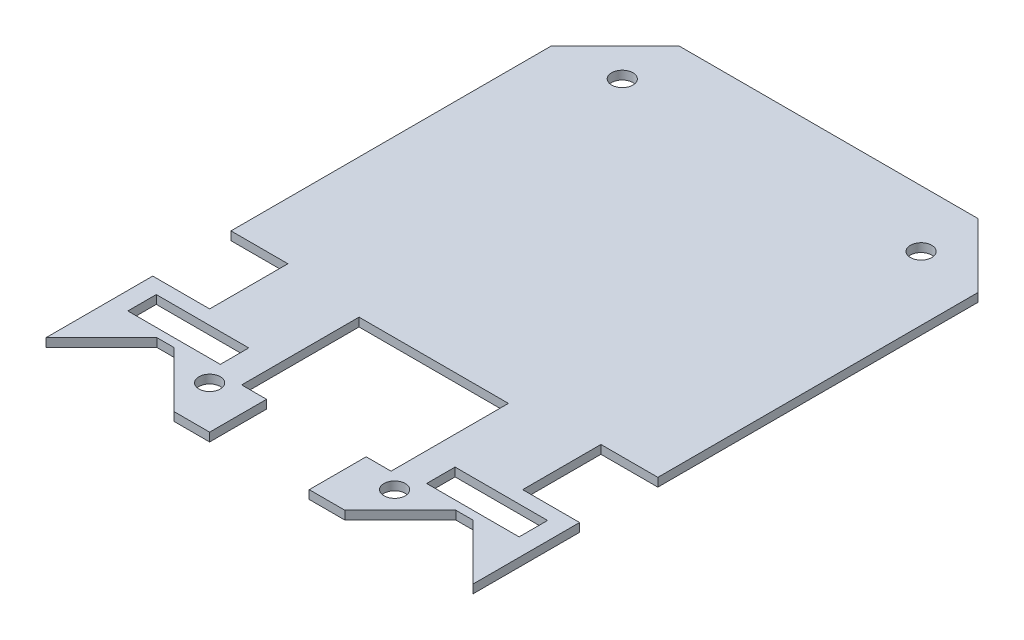
SolidWorks part; units mm, degrees
ref_plane "Front Plane" through (0, 0, 0) normal (0, 0, 1) x (1, 0, 0)
ref_plane "Top Plane" through (0, 0, 0) normal (0, 1, 0) x (1, 0, 0)
ref_plane "Right Plane" through (0, 0, 0) normal (1, 0, 0) x (0, 0, -1)
sketch "Sketch1" plane through (0, 0, 0) normal (0, 1, 0) x (1, 0, 0)
  line L0 (-30, -25) -> (-30, -40)
  line L1 (-30, 40) -> (30, 40)
  line L2 (-30, 40) -> (-30, -14)
  line L3 (-30, -40) -> (30, -40)
  line L4 (30, 40) -> (30, -14)
  line L5 (-30, -25) -> (-22, -25)
  line L6 (30, -25) -> (30, -40)
  line L7 (-30, -14) -> (-22, -14)
  line L8 (22, -25) -> (22, -14)
  line L9 (30, -25) -> (22, -25)
  line L10 (-22, -25) -> (-22, -14)
  line L11 (30, -14) -> (22, -14)
  line L13 (30, -40) -> (-30, 40) construction
  point P12 (0, 0)
  dimension "D1" = 60
  dimension "D2" = 15
  dimension "D3" = 11
  dimension "D4" = 80
  dimension "D5" = 8
  dimension "D6" = 11
  dimension "D7" = 8
  dimension "D8" = 15
  dimension "D9" = 8
  dimension "D10" = 8
extrude "Extrude1" add sketch "Sketch1" along normal blind 1.2
chamfer "Chamfer1" distance 9 angle 45 2 edges at (-30, 0.6, -40) (30, 0.6, -40)
hole_wizard "Ø3.0 (3) Diameter Hole1" positions "3DSketch1" profile "Sketch3" hole size "Ø3.0" standard "DIN"
sketch3d "3DSketch1"
  line L1 (-30, 1.2, -31) -> (-30, 1.2, 14) construction
  line L4 (30, 1.2, 14) -> (30, 1.2, -31) construction
  line L6 (-30, 1.2, 40) -> (30, 1.2, 40) construction
  line L7 (21, 1.2, -32) -> (59.767, 1.2, -32) construction
  line L9 (30, 1.2, 40) -> (30, 1.2, 25) construction
  point P0 (-13, 1.2, 34)
  point P2 (13, 1.2, 34)
  point P4 (21, 1.2, -32)
  point P6 (-21, 1.2, -32)
  dimension "D1" = 17
  dimension "D2" = 6
  dimension "D6" = 66
  dimension "D3" = 17
  dimension "D5" = 9
  dimension "D7" = 9
sketch "Sketch3" plane through (-13, 1.2, 34) normal (1, 0, 0) x (0, 0, 1)
  line L0 (0, 0) -> (0, 10.9013)
  line L1 (0, 10.9013) -> (1.5, 10)
  line L2 (1.5, 10) -> (1.5, 0)
  line L5 (1.5, 0) -> (0, 0)
  line L10 (0, 10.9013) -> (-1.5, 10) construction
  line L11 (0, -6.35) -> (0, 107.95) construction
  dimension "Hole Dia." = 3
  dimension "Hole Depth" = 10
  dimension "Drill Angle" = 118
sketch "Sketch4" plane through (0, 1.2, 0) normal (0, 1, 0) x (1, 0, 0)
  line L0 (0, -61.9095) -> (0, -36.4705) construction
  line L1 (-10.5, -32) -> (-7, -32)
  line L2 (-10.5, -32) -> (-10.5, -15.5)
  line L3 (-10.5, -15.5) -> (10.5, -15.5)
  line L4 (10.5, -32) -> (10.5, -15.5)
  line L5 (-30, -40) -> (30, -40) construction
  line L6 (7, -32) -> (10.5, -32)
  line L7 (-30, -40) -> (30, -40) construction
  line L8 (-7, -32) -> (-7, -40)
  line L9 (-7, -40) -> (7, -40)
  line L10 (7, -32) -> (7, -40)
  point P8 (0, -40)
  point P9 (0, -40)
  point P15 (0, -15.5)
  dimension "D1" = 21
  dimension "D2" = 16.5
  dimension "D3" = 14
  dimension "D4" = 8
extrude "Cut-Extrude1" cut sketch "Sketch4" against normal blind 10
sketch "Sketch5" plane through (0, 1.2, 0) normal (0, 1, 0) x (1, 0, 0)
  line L1 (14.5, -31) -> (27.5, -31)
  line L2 (14.5, -31) -> (14.5, -27)
  line L3 (14.5, -27) -> (27.5, -27)
  line L4 (27.5, -31) -> (27.5, -27)
  line L7 (0, 0) -> (0, -55.2953) construction
  line L8 (-27.5, -31) -> (-27.5, -27)
  line L9 (-14.5, -27) -> (-27.5, -27)
  line L10 (-14.5, -31) -> (-14.5, -27)
  line L11 (-14.5, -31) -> (-27.5, -31)
  line L12 (7, -40) -> (30, -40) construction
  line L13 (30, -40) -> (30, -25) construction
  dimension "D1" = 9
  dimension "D2" = 2.5
  dimension "D3" = 4
  dimension "D4" = 13
extrude "Cut-Extrude2" cut sketch "Sketch5" against normal blind 10
sketch "Sketch6" plane through (0, 1.2, 0) normal (0, 1, 0) x (1, 0, 0)
  line L0 (12, -40) -> (19.8, -32.2)
  line L1 (22.2, -32.2) -> (30, -40)
  line L2 (30, -40) -> (30, -25) construction
  line L3 (19.8, -32.2) -> (22.2, -32.2)
  line L4 (21, -31) -> (21, -43.054) construction
  line L5 (14.5, -31) -> (27.5, -31) construction
  line L6 (30, -40) -> (12, -40)
  line L7 (0, 0) -> (0, -57.0248) construction
  line L8 (-21, -31) -> (-21, -43.054) construction
  line L9 (-30, -40) -> (-12, -40)
  line L10 (-19.8, -32.2) -> (-22.2, -32.2)
  line L11 (-22.2, -32.2) -> (-30, -40)
  line L12 (-12, -40) -> (-19.8, -32.2)
  line L14 (7, -40) -> (30, -40) construction
  point P10 (21, -32.2)
  dimension "D1" = 45
  dimension "D2" = 1.2
  dimension "D3" = 18
extrude "Cut-Extrude3" cut sketch "Sketch6" against normal blind 10
